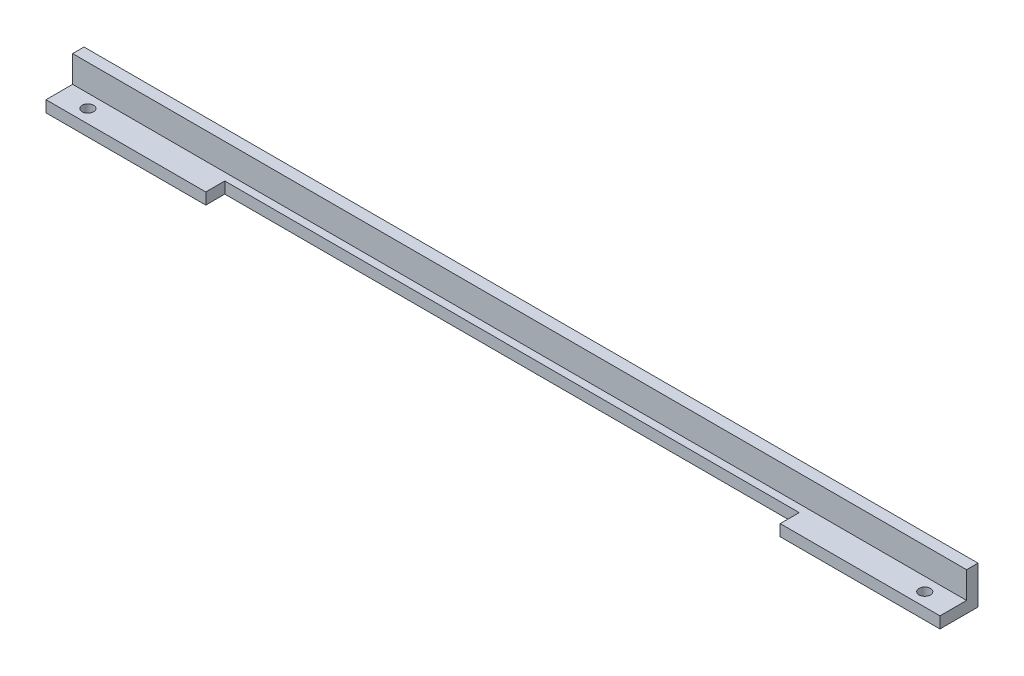
SolidWorks part; units mm, degrees
ref_plane "Спереди" through (0, 0, 0) normal (0, 0, 1) x (1, 0, 0)
ref_plane "Сверху" through (0, 0, 0) normal (0, 1, 0) x (1, 0, 0)
ref_plane "Справа" through (0, 0, 0) normal (1, 0, 0) x (0, 0, -1)
sketch "Эскиз1" plane through (0, 0, 0) normal (1, 0, 0) x (0, 0, -1)
  line L0 (0, 0) -> (-10, 0)
  line L1 (-10, 0) -> (-10, 3)
  line L2 (-10, 3) -> (-3, 3)
  line L3 (-3, 10) -> (-3, 3)
  line L6 (-3, 10) -> (0, 10)
  line L7 (0, 10) -> (0, 0)
  dimension "D1" = 3
  dimension "D2" = 10
extrude "Бобышка-Вытянуть1" add sketch "Эскиз1" along normal blind 235
sketch "Эскиз3" plane through (0, 3, 0) normal (0, 1, 0) x (1, 0, 0)
  line L0 (0, -3) -> (0, -10) construction
  line L1 (235, -10) -> (0, -10) construction
  line L2 (117.5, -10) -> (117.5, 0) construction
  line L3 (235, 0) -> (0, 0) construction
  circle A0 centre (7.5, -6.5) radius 1.5
  circle A1 centre (227.5, -6.5) radius 1.5
  dimension "D1" = 3
  dimension "D2" = 7.5
  dimension "D3" = 3.5
extrude "Вырез-Вытянуть1" cut sketch "Эскиз3" against normal blind 10
sketch "Эскиз4" plane through (0, 0, 10) normal (0, 0, 1) x (1, 0, 0)
  line L0 (42, 0) -> (42, 3)
  line L1 (235, 0) -> (0, 0) construction
  line L2 (235, 3) -> (0, 3) construction
  line L3 (0, 3) -> (0, 0) construction
  line L4 (117.5, 0) -> (117.5, 3) construction
  line L5 (235, 3) -> (0, 3) construction
  line L6 (193, 0) -> (193, 3)
  line L7 (42, 3) -> (193, 3)
  line L8 (193, 0) -> (42, 0)
  dimension "D1" = 42
extrude "Вырез-Вытянуть2" cut sketch "Эскиз4" against normal blind 5
